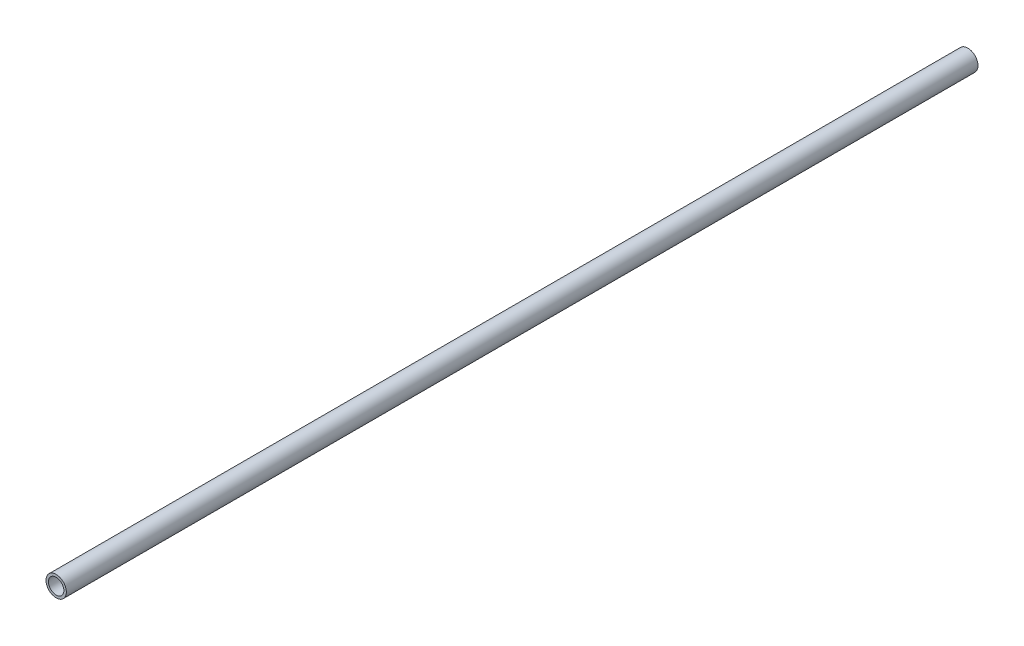
SolidWorks part; units mm, degrees
ref_plane "Alzado" through (0, 0, 0) normal (0, 0, 1) x (1, 0, 0)
ref_plane "Planta" through (0, 0, 0) normal (0, 1, 0) x (1, 0, 0)
ref_plane "Vista lateral" through (0, 0, 0) normal (1, 0, 0) x (0, 0, -1)
sketch "Croquis1" plane through (0, 0, 0) normal (0, 0, 1) x (1, 0, 0)
  circle A0 centre (0, 0) radius 16.75
  dimension "D1" = 33.5
extrude "Saliente-Extruir1" add sketch "Croquis1" along normal blind 1500
ref_plane "Plano1" through (0, 0, 1500) normal (0, 0, 1) x (1, 0, 0)
sketch "Croquis2" plane through (0, 0, 1500) normal (0, 0, 1) x (1, 0, 0)
  circle A0 centre (0, 0) radius 12.7
  dimension "D1" = 25.4
extrude "Cortar-Extruir1" cut sketch "Croquis2" against normal blind 1500
